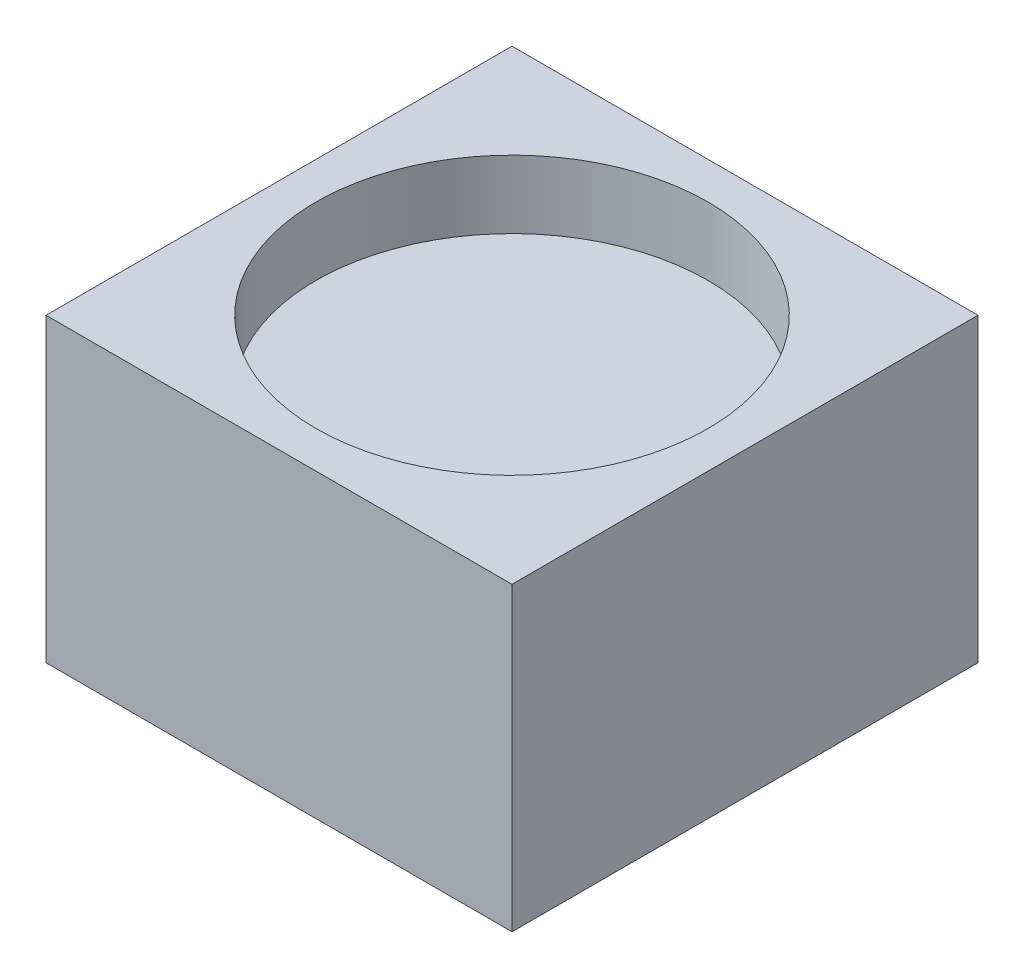
SolidWorks part; units mm, degrees
ref_plane "Front Plane" through (0, 0, 0) normal (0, 0, 1) x (1, 0, 0)
ref_plane "Top Plane" through (0, 0, 0) normal (0, 1, 0) x (1, 0, 0)
ref_plane "Right Plane" through (0, 0, 0) normal (1, 0, 0) x (0, 0, -1)
sketch "Sketch1" plane through (0, 0, 0) normal (0, 1, 0) x (1, 0, 0)
  line L1 (-76.2, -76.2) -> (76.2, -76.2)
  line L2 (-76.2, -76.2) -> (-76.2, 76.2)
  line L3 (-76.2, 76.2) -> (76.2, 76.2)
  line L4 (76.2, -76.2) -> (76.2, 76.2)
  line L5 (-76.2, -76.2) -> (76.2, 76.2) construction
  line L6 (-76.2, 76.2) -> (76.2, -76.2) construction
  circle A0 centre (0, 0) radius 64.135
  dimension "D1" = 128.27
  dimension "D2" = 152.4
  dimension "D3" = 152.4
extrude "Boss-Extrude1" add sketch "Sketch1" along normal blind 22.225
sketch "Sketch2" plane through (0, 0, 0) normal (0, -1, 0) x (-1, 0, 0)
  line L1 (76.2, -76.2) -> (-76.2, -76.2)
  line L2 (76.2, -76.2) -> (76.2, 76.2)
  line L3 (76.2, 76.2) -> (-76.2, 76.2)
  line L4 (-76.2, -76.2) -> (-76.2, 76.2)
extrude "Boss-Extrude2" add sketch "Sketch2" along normal blind 76.2
